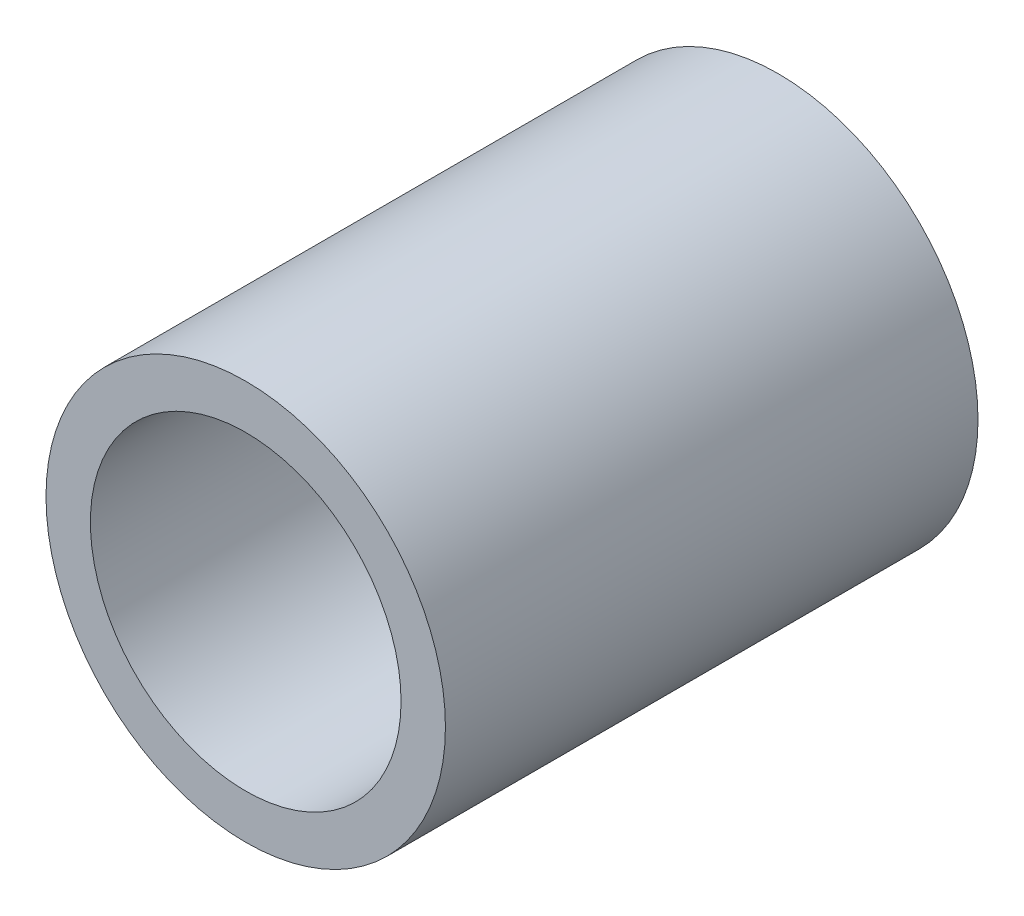
SolidWorks part; units mm, degrees
material "3003 Alloy"
ref_plane "Front Plane" through (0, 0, 0) normal (0, 0, 1) x (1, 0, 0)
ref_plane "Top Plane" through (0, 0, 0) normal (0, 1, 0) x (1, 0, 0)
ref_plane "Right Plane" through (0, 0, 0) normal (1, 0, 0) x (0, 0, -1)
sketch "Sketch1" plane through (0, 0, 0) normal (0, 0, 1) x (1, 0, 0)
  circle A0 centre (0, 0) radius 3.5
  dimension "D1" = 7
extrude "Extrude1" add sketch "Sketch1" along normal blind 12
shell "Shell1" thickness 1
